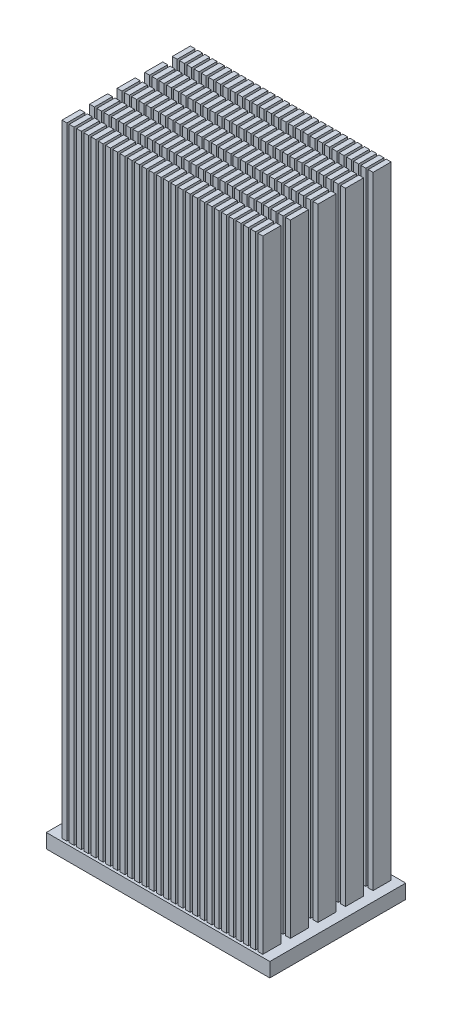
SolidWorks part; units mm, degrees
ref_plane "Front" through (0, 0, 0) normal (0, 0, 1) x (1, 0, 0)
ref_plane "Top" through (0, 0, 0) normal (0, 1, 0) x (1, 0, 0)
ref_plane "Right" through (0, 0, 0) normal (1, 0, 0) x (0, 0, -1)
sketch "Sketch1" plane through (0, 0, 0) normal (0, 1, 0) x (1, 0, 0)
  line L1 (39.12, -23.785) -> (-39.12, -23.785)
  line L2 (39.12, -23.785) -> (39.12, 23.785)
  line L3 (39.12, 23.785) -> (-39.12, 23.785)
  line L4 (-39.12, -23.785) -> (-39.12, 23.785)
  line L5 (39.12, -23.785) -> (-39.12, 23.785) construction
  line L6 (39.12, 23.785) -> (-39.12, -23.785) construction
  point P0 (0, 0)
  dimension "D1" = 47.57
  dimension "D2" = 78.24
extrude "Boss-Extrude1" add sketch "Sketch1" along normal blind 5
sketch "Sketch2" plane through (0, 0, 0) normal (0, 1, 0) x (1, 0, 0)
  line L0 (-30.3233, 22.0914) -> (-32.0273, 15.7622) construction
  line L1 (-32.8633, 22.0914) -> (-34.5673, 22.0914)
  line L2 (-32.8633, 22.0914) -> (-32.8633, 15.7622)
  line L3 (-32.8633, 15.7622) -> (-34.5673, 15.7622)
  line L4 (-34.5673, 22.0914) -> (-34.5673, 15.7622)
  line L5 (-32.8633, 22.0914) -> (-34.5673, 15.7622) construction
  line L6 (-32.8633, 15.7622) -> (-34.5673, 22.0914) construction
  line L7 (-30.3233, 15.7622) -> (-32.0273, 22.0914) construction
  line L8 (-30.3233, 22.0914) -> (-30.3233, 15.7622)
  line L9 (-30.3233, 22.0914) -> (-32.0273, 22.0914)
  line L10 (-32.0273, 22.0914) -> (-32.0273, 15.7622)
  line L11 (-30.3233, 15.7622) -> (-32.0273, 15.7622)
  line L12 (-27.7833, 22.0914) -> (-29.4873, 15.7622) construction
  line L13 (-27.7833, 15.7622) -> (-29.4873, 22.0914) construction
  line L14 (-27.7833, 22.0914) -> (-27.7833, 15.7622)
  line L15 (-27.7833, 22.0914) -> (-29.4873, 22.0914)
  line L16 (-29.4873, 22.0914) -> (-29.4873, 15.7622)
  line L17 (-27.7833, 15.7622) -> (-29.4873, 15.7622)
  line L18 (-25.2433, 22.0914) -> (-26.9473, 15.7622) construction
  line L19 (-25.2433, 15.7622) -> (-26.9473, 22.0914) construction
  line L20 (-25.2433, 22.0914) -> (-25.2433, 15.7622)
  line L21 (-25.2433, 22.0914) -> (-26.9473, 22.0914)
  line L22 (-26.9473, 22.0914) -> (-26.9473, 15.7622)
  line L23 (-25.2433, 15.7622) -> (-26.9473, 15.7622)
  line L24 (-22.7033, 22.0914) -> (-24.4073, 15.7622) construction
  line L25 (-22.7033, 15.7622) -> (-24.4073, 22.0914) construction
  line L26 (-22.7033, 22.0914) -> (-22.7033, 15.7622)
  line L27 (-22.7033, 22.0914) -> (-24.4073, 22.0914)
  line L28 (-24.4073, 22.0914) -> (-24.4073, 15.7622)
  line L29 (-22.7033, 15.7622) -> (-24.4073, 15.7622)
  line L30 (-20.1633, 22.0914) -> (-21.8673, 15.7622) construction
  line L31 (-20.1633, 15.7622) -> (-21.8673, 22.0914) construction
  line L32 (-20.1633, 22.0914) -> (-20.1633, 15.7622)
  line L33 (-20.1633, 22.0914) -> (-21.8673, 22.0914)
  line L34 (-21.8673, 22.0914) -> (-21.8673, 15.7622)
  line L35 (-20.1633, 15.7622) -> (-21.8673, 15.7622)
  line L36 (-17.6233, 22.0914) -> (-19.3273, 15.7622) construction
  line L37 (-17.6233, 15.7622) -> (-19.3273, 22.0914) construction
  line L38 (-17.6233, 22.0914) -> (-17.6233, 15.7622)
  line L39 (-17.6233, 22.0914) -> (-19.3273, 22.0914)
  line L40 (-19.3273, 22.0914) -> (-19.3273, 15.7622)
  line L41 (-17.6233, 15.7622) -> (-19.3273, 15.7622)
  line L42 (-15.0833, 22.0914) -> (-16.7873, 15.7622) construction
  line L43 (-15.0833, 15.7622) -> (-16.7873, 22.0914) construction
  line L44 (-15.0833, 22.0914) -> (-15.0833, 15.7622)
  line L45 (-15.0833, 22.0914) -> (-16.7873, 22.0914)
  line L46 (-16.7873, 22.0914) -> (-16.7873, 15.7622)
  line L47 (-15.0833, 15.7622) -> (-16.7873, 15.7622)
  line L48 (-12.5433, 22.0914) -> (-14.2473, 15.7622) construction
  line L49 (-12.5433, 15.7622) -> (-14.2473, 22.0914) construction
  line L50 (-12.5433, 22.0914) -> (-12.5433, 15.7622)
  line L51 (-12.5433, 22.0914) -> (-14.2473, 22.0914)
  line L52 (-14.2473, 22.0914) -> (-14.2473, 15.7622)
  line L53 (-12.5433, 15.7622) -> (-14.2473, 15.7622)
  line L54 (-10.0033, 22.0914) -> (-11.7073, 15.7622) construction
  line L55 (-10.0033, 15.7622) -> (-11.7073, 22.0914) construction
  line L56 (-10.0033, 22.0914) -> (-10.0033, 15.7622)
  line L57 (-10.0033, 22.0914) -> (-11.7073, 22.0914)
  line L58 (-11.7073, 22.0914) -> (-11.7073, 15.7622)
  line L59 (-10.0033, 15.7622) -> (-11.7073, 15.7622)
  line L60 (-7.4633, 22.0914) -> (-9.1673, 15.7622) construction
  line L61 (-7.4633, 15.7622) -> (-9.1673, 22.0914) construction
  line L62 (-7.4633, 22.0914) -> (-7.4633, 15.7622)
  line L63 (-7.4633, 22.0914) -> (-9.1673, 22.0914)
  line L64 (-9.1673, 22.0914) -> (-9.1673, 15.7622)
  line L65 (-7.4633, 15.7622) -> (-9.1673, 15.7622)
  line L66 (-4.9233, 22.0914) -> (-6.6273, 15.7622) construction
  line L67 (-4.9233, 15.7622) -> (-6.6273, 22.0914) construction
  line L68 (-4.9233, 22.0914) -> (-4.9233, 15.7622)
  line L69 (-4.9233, 22.0914) -> (-6.6273, 22.0914)
  line L70 (-6.6273, 22.0914) -> (-6.6273, 15.7622)
  line L71 (-4.9233, 15.7622) -> (-6.6273, 15.7622)
  line L72 (-2.3833, 22.0914) -> (-4.0873, 15.7622) construction
  line L73 (-2.3833, 15.7622) -> (-4.0873, 22.0914) construction
  line L74 (-2.3833, 22.0914) -> (-2.3833, 15.7622)
  line L75 (-2.3833, 22.0914) -> (-4.0873, 22.0914)
  line L76 (-4.0873, 22.0914) -> (-4.0873, 15.7622)
  line L77 (-2.3833, 15.7622) -> (-4.0873, 15.7622)
  line L78 (0.1567, 22.0914) -> (-1.5473, 15.7622) construction
  line L79 (0.1567, 15.7622) -> (-1.5473, 22.0914) construction
  line L80 (0.1567, 22.0914) -> (0.1567, 15.7622)
  line L81 (0.1567, 22.0914) -> (-1.5473, 22.0914)
  line L82 (-1.5473, 22.0914) -> (-1.5473, 15.7622)
  line L83 (0.1567, 15.7622) -> (-1.5473, 15.7622)
  line L84 (2.6967, 22.0914) -> (0.9927, 15.7622) construction
  line L85 (2.6967, 15.7622) -> (0.9927, 22.0914) construction
  line L86 (2.6967, 22.0914) -> (2.6967, 15.7622)
  line L87 (2.6967, 22.0914) -> (0.9927, 22.0914)
  line L88 (0.9927, 22.0914) -> (0.9927, 15.7622)
  line L89 (2.6967, 15.7622) -> (0.9927, 15.7622)
  line L90 (5.2367, 22.0914) -> (3.5327, 15.7622) construction
  line L91 (5.2367, 15.7622) -> (3.5327, 22.0914) construction
  line L92 (5.2367, 22.0914) -> (5.2367, 15.7622)
  line L93 (5.2367, 22.0914) -> (3.5327, 22.0914)
  line L94 (3.5327, 22.0914) -> (3.5327, 15.7622)
  line L95 (5.2367, 15.7622) -> (3.5327, 15.7622)
  line L96 (7.7767, 22.0914) -> (6.0727, 15.7622) construction
  line L97 (7.7767, 15.7622) -> (6.0727, 22.0914) construction
  line L98 (7.7767, 22.0914) -> (7.7767, 15.7622)
  line L99 (7.7767, 22.0914) -> (6.0727, 22.0914)
  line L100 (6.0727, 22.0914) -> (6.0727, 15.7622)
  line L101 (7.7767, 15.7622) -> (6.0727, 15.7622)
  line L102 (10.3167, 22.0914) -> (8.6127, 15.7622) construction
  line L103 (10.3167, 15.7622) -> (8.6127, 22.0914) construction
  line L104 (10.3167, 22.0914) -> (10.3167, 15.7622)
  line L105 (10.3167, 22.0914) -> (8.6127, 22.0914)
  line L106 (8.6127, 22.0914) -> (8.6127, 15.7622)
  line L107 (10.3167, 15.7622) -> (8.6127, 15.7622)
  line L108 (12.8567, 22.0914) -> (11.1527, 15.7622) construction
  line L109 (12.8567, 15.7622) -> (11.1527, 22.0914) construction
  line L110 (12.8567, 22.0914) -> (12.8567, 15.7622)
  line L111 (12.8567, 22.0914) -> (11.1527, 22.0914)
  line L112 (11.1527, 22.0914) -> (11.1527, 15.7622)
  line L113 (12.8567, 15.7622) -> (11.1527, 15.7622)
  line L114 (15.3967, 22.0914) -> (13.6927, 15.7622) construction
  line L115 (15.3967, 15.7622) -> (13.6927, 22.0914) construction
  line L116 (15.3967, 22.0914) -> (15.3967, 15.7622)
  line L117 (15.3967, 22.0914) -> (13.6927, 22.0914)
  line L118 (13.6927, 22.0914) -> (13.6927, 15.7622)
  line L119 (15.3967, 15.7622) -> (13.6927, 15.7622)
  line L120 (17.9367, 22.0914) -> (16.2327, 15.7622) construction
  line L121 (17.9367, 15.7622) -> (16.2327, 22.0914) construction
  line L122 (17.9367, 22.0914) -> (17.9367, 15.7622)
  line L123 (17.9367, 22.0914) -> (16.2327, 22.0914)
  line L124 (16.2327, 22.0914) -> (16.2327, 15.7622)
  line L125 (17.9367, 15.7622) -> (16.2327, 15.7622)
  line L126 (20.4767, 22.0914) -> (18.7727, 15.7622) construction
  line L127 (20.4767, 15.7622) -> (18.7727, 22.0914) construction
  line L128 (20.4767, 22.0914) -> (20.4767, 15.7622)
  line L129 (20.4767, 22.0914) -> (18.7727, 22.0914)
  line L130 (18.7727, 22.0914) -> (18.7727, 15.7622)
  line L131 (20.4767, 15.7622) -> (18.7727, 15.7622)
  line L132 (23.0167, 22.0914) -> (21.3127, 15.7622) construction
  line L133 (23.0167, 15.7622) -> (21.3127, 22.0914) construction
  line L134 (23.0167, 22.0914) -> (23.0167, 15.7622)
  line L135 (23.0167, 22.0914) -> (21.3127, 22.0914)
  line L136 (21.3127, 22.0914) -> (21.3127, 15.7622)
  line L137 (23.0167, 15.7622) -> (21.3127, 15.7622)
  line L138 (25.5567, 22.0914) -> (23.8527, 15.7622) construction
  line L139 (25.5567, 15.7622) -> (23.8527, 22.0914) construction
  line L140 (25.5567, 22.0914) -> (25.5567, 15.7622)
  line L141 (25.5567, 22.0914) -> (23.8527, 22.0914)
  line L142 (23.8527, 22.0914) -> (23.8527, 15.7622)
  line L143 (25.5567, 15.7622) -> (23.8527, 15.7622)
  line L144 (28.0967, 22.0914) -> (26.3927, 15.7622) construction
  line L145 (28.0967, 15.7622) -> (26.3927, 22.0914) construction
  line L146 (28.0967, 22.0914) -> (28.0967, 15.7622)
  line L147 (28.0967, 22.0914) -> (26.3927, 22.0914)
  line L148 (26.3927, 22.0914) -> (26.3927, 15.7622)
  line L149 (28.0967, 15.7622) -> (26.3927, 15.7622)
  line L150 (30.6367, 22.0914) -> (28.9327, 15.7622) construction
  line L151 (30.6367, 15.7622) -> (28.9327, 22.0914) construction
  line L152 (30.6367, 22.0914) -> (30.6367, 15.7622)
  line L153 (30.6367, 22.0914) -> (28.9327, 22.0914)
  line L154 (28.9327, 22.0914) -> (28.9327, 15.7622)
  line L155 (30.6367, 15.7622) -> (28.9327, 15.7622)
  line L156 (33.1767, 22.0914) -> (31.4727, 15.7622) construction
  line L157 (33.1767, 15.7622) -> (31.4727, 22.0914) construction
  line L158 (33.1767, 22.0914) -> (33.1767, 15.7622)
  line L159 (33.1767, 22.0914) -> (31.4727, 22.0914)
  line L160 (31.4727, 22.0914) -> (31.4727, 15.7622)
  line L161 (33.1767, 15.7622) -> (31.4727, 15.7622)
  line L162 (35.7167, 22.0914) -> (34.0127, 15.7622) construction
  line L163 (35.7167, 15.7622) -> (34.0127, 22.0914) construction
  line L164 (35.7167, 22.0914) -> (35.7167, 15.7622)
  line L165 (35.7167, 22.0914) -> (34.0127, 22.0914)
  line L166 (34.0127, 22.0914) -> (34.0127, 15.7622)
  line L167 (35.7167, 15.7622) -> (34.0127, 15.7622)
  line L168 (-30.3233, 12.4394) -> (-32.0273, 6.1102) construction
  line L169 (-30.3233, 6.1102) -> (-32.0273, 12.4394) construction
  line L170 (-30.3233, 12.4394) -> (-30.3233, 6.1102)
  line L171 (-30.3233, 12.4394) -> (-32.0273, 12.4394)
  line L172 (-32.0273, 12.4394) -> (-32.0273, 6.1102)
  line L173 (-30.3233, 6.1102) -> (-32.0273, 6.1102)
  line L174 (-27.7833, 12.4394) -> (-29.4873, 6.1102) construction
  line L175 (-27.7833, 6.1102) -> (-29.4873, 12.4394) construction
  line L176 (-27.7833, 12.4394) -> (-27.7833, 6.1102)
  line L177 (-27.7833, 12.4394) -> (-29.4873, 12.4394)
  line L178 (-29.4873, 12.4394) -> (-29.4873, 6.1102)
  line L179 (-27.7833, 6.1102) -> (-29.4873, 6.1102)
  line L180 (-25.2433, 12.4394) -> (-26.9473, 6.1102) construction
  line L181 (-25.2433, 6.1102) -> (-26.9473, 12.4394) construction
  line L182 (-25.2433, 12.4394) -> (-25.2433, 6.1102)
  line L183 (-25.2433, 12.4394) -> (-26.9473, 12.4394)
  line L184 (-26.9473, 12.4394) -> (-26.9473, 6.1102)
  line L185 (-25.2433, 6.1102) -> (-26.9473, 6.1102)
  line L186 (-22.7033, 12.4394) -> (-24.4073, 6.1102) construction
  line L187 (-22.7033, 6.1102) -> (-24.4073, 12.4394) construction
  line L188 (-22.7033, 12.4394) -> (-22.7033, 6.1102)
  line L189 (-22.7033, 12.4394) -> (-24.4073, 12.4394)
  line L190 (-24.4073, 12.4394) -> (-24.4073, 6.1102)
  line L191 (-22.7033, 6.1102) -> (-24.4073, 6.1102)
  line L192 (-20.1633, 12.4394) -> (-21.8673, 6.1102) construction
  line L193 (-20.1633, 6.1102) -> (-21.8673, 12.4394) construction
  line L194 (-20.1633, 12.4394) -> (-20.1633, 6.1102)
  line L195 (-20.1633, 12.4394) -> (-21.8673, 12.4394)
  line L196 (-21.8673, 12.4394) -> (-21.8673, 6.1102)
  line L197 (-20.1633, 6.1102) -> (-21.8673, 6.1102)
  line L198 (-17.6233, 12.4394) -> (-19.3273, 6.1102) construction
  line L199 (-17.6233, 6.1102) -> (-19.3273, 12.4394) construction
  line L200 (-17.6233, 12.4394) -> (-17.6233, 6.1102)
  line L201 (-17.6233, 12.4394) -> (-19.3273, 12.4394)
  line L202 (-19.3273, 12.4394) -> (-19.3273, 6.1102)
  line L203 (-17.6233, 6.1102) -> (-19.3273, 6.1102)
  line L204 (-15.0833, 12.4394) -> (-16.7873, 6.1102) construction
  line L205 (-15.0833, 6.1102) -> (-16.7873, 12.4394) construction
  line L206 (-15.0833, 12.4394) -> (-15.0833, 6.1102)
  line L207 (-15.0833, 12.4394) -> (-16.7873, 12.4394)
  line L208 (-16.7873, 12.4394) -> (-16.7873, 6.1102)
  line L209 (-15.0833, 6.1102) -> (-16.7873, 6.1102)
  line L210 (-12.5433, 12.4394) -> (-14.2473, 6.1102) construction
  line L211 (-12.5433, 6.1102) -> (-14.2473, 12.4394) construction
  line L212 (-12.5433, 12.4394) -> (-12.5433, 6.1102)
  line L213 (-12.5433, 12.4394) -> (-14.2473, 12.4394)
  line L214 (-14.2473, 12.4394) -> (-14.2473, 6.1102)
  line L215 (-12.5433, 6.1102) -> (-14.2473, 6.1102)
  line L216 (-10.0033, 12.4394) -> (-11.7073, 6.1102) construction
  line L217 (-10.0033, 6.1102) -> (-11.7073, 12.4394) construction
  line L218 (-10.0033, 12.4394) -> (-10.0033, 6.1102)
  line L219 (-10.0033, 12.4394) -> (-11.7073, 12.4394)
  line L220 (-11.7073, 12.4394) -> (-11.7073, 6.1102)
  line L221 (-10.0033, 6.1102) -> (-11.7073, 6.1102)
  line L222 (-7.4633, 12.4394) -> (-9.1673, 6.1102) construction
  line L223 (-7.4633, 6.1102) -> (-9.1673, 12.4394) construction
  line L224 (-7.4633, 12.4394) -> (-7.4633, 6.1102)
  line L225 (-7.4633, 12.4394) -> (-9.1673, 12.4394)
  line L226 (-9.1673, 12.4394) -> (-9.1673, 6.1102)
  line L227 (-7.4633, 6.1102) -> (-9.1673, 6.1102)
  line L228 (-4.9233, 12.4394) -> (-6.6273, 6.1102) construction
  line L229 (-4.9233, 6.1102) -> (-6.6273, 12.4394) construction
  line L230 (-4.9233, 12.4394) -> (-4.9233, 6.1102)
  line L231 (-4.9233, 12.4394) -> (-6.6273, 12.4394)
  line L232 (-6.6273, 12.4394) -> (-6.6273, 6.1102)
  line L233 (-4.9233, 6.1102) -> (-6.6273, 6.1102)
  line L234 (-2.3833, 12.4394) -> (-4.0873, 6.1102) construction
  line L235 (-2.3833, 6.1102) -> (-4.0873, 12.4394) construction
  line L236 (-2.3833, 12.4394) -> (-2.3833, 6.1102)
  line L237 (-2.3833, 12.4394) -> (-4.0873, 12.4394)
  line L238 (-4.0873, 12.4394) -> (-4.0873, 6.1102)
  line L239 (-2.3833, 6.1102) -> (-4.0873, 6.1102)
  line L240 (0.1567, 12.4394) -> (-1.5473, 6.1102) construction
  line L241 (0.1567, 6.1102) -> (-1.5473, 12.4394) construction
  line L242 (0.1567, 12.4394) -> (0.1567, 6.1102)
  line L243 (0.1567, 12.4394) -> (-1.5473, 12.4394)
  line L244 (-1.5473, 12.4394) -> (-1.5473, 6.1102)
  line L245 (0.1567, 6.1102) -> (-1.5473, 6.1102)
  line L246 (2.6967, 12.4394) -> (0.9927, 6.1102) construction
  line L247 (2.6967, 6.1102) -> (0.9927, 12.4394) construction
  line L248 (2.6967, 12.4394) -> (2.6967, 6.1102)
  line L249 (2.6967, 12.4394) -> (0.9927, 12.4394)
  line L250 (0.9927, 12.4394) -> (0.9927, 6.1102)
  line L251 (2.6967, 6.1102) -> (0.9927, 6.1102)
  line L252 (5.2367, 12.4394) -> (3.5327, 6.1102) construction
  line L253 (5.2367, 6.1102) -> (3.5327, 12.4394) construction
  line L254 (5.2367, 12.4394) -> (5.2367, 6.1102)
  line L255 (5.2367, 12.4394) -> (3.5327, 12.4394)
  line L256 (3.5327, 12.4394) -> (3.5327, 6.1102)
  line L257 (5.2367, 6.1102) -> (3.5327, 6.1102)
  line L258 (7.7767, 12.4394) -> (6.0727, 6.1102) construction
  line L259 (7.7767, 6.1102) -> (6.0727, 12.4394) construction
  line L260 (7.7767, 12.4394) -> (7.7767, 6.1102)
  line L261 (7.7767, 12.4394) -> (6.0727, 12.4394)
  line L262 (6.0727, 12.4394) -> (6.0727, 6.1102)
  line L263 (7.7767, 6.1102) -> (6.0727, 6.1102)
  line L264 (10.3167, 12.4394) -> (8.6127, 6.1102) construction
  line L265 (10.3167, 6.1102) -> (8.6127, 12.4394) construction
  line L266 (10.3167, 12.4394) -> (10.3167, 6.1102)
  line L267 (10.3167, 12.4394) -> (8.6127, 12.4394)
  line L268 (8.6127, 12.4394) -> (8.6127, 6.1102)
  line L269 (10.3167, 6.1102) -> (8.6127, 6.1102)
  line L270 (12.8567, 12.4394) -> (11.1527, 6.1102) construction
  line L271 (12.8567, 6.1102) -> (11.1527, 12.4394) construction
  line L272 (12.8567, 12.4394) -> (12.8567, 6.1102)
  line L273 (12.8567, 12.4394) -> (11.1527, 12.4394)
  line L274 (11.1527, 12.4394) -> (11.1527, 6.1102)
  line L275 (12.8567, 6.1102) -> (11.1527, 6.1102)
  line L276 (15.3967, 12.4394) -> (13.6927, 6.1102) construction
  line L277 (15.3967, 6.1102) -> (13.6927, 12.4394) construction
  line L278 (15.3967, 12.4394) -> (15.3967, 6.1102)
  line L279 (15.3967, 12.4394) -> (13.6927, 12.4394)
  line L280 (13.6927, 12.4394) -> (13.6927, 6.1102)
  line L281 (15.3967, 6.1102) -> (13.6927, 6.1102)
  line L282 (17.9367, 12.4394) -> (16.2327, 6.1102) construction
  line L283 (17.9367, 6.1102) -> (16.2327, 12.4394) construction
  line L284 (17.9367, 12.4394) -> (17.9367, 6.1102)
  line L285 (17.9367, 12.4394) -> (16.2327, 12.4394)
  line L286 (16.2327, 12.4394) -> (16.2327, 6.1102)
  line L287 (17.9367, 6.1102) -> (16.2327, 6.1102)
  line L288 (20.4767, 12.4394) -> (18.7727, 6.1102) construction
  line L289 (20.4767, 6.1102) -> (18.7727, 12.4394) construction
  line L290 (20.4767, 12.4394) -> (20.4767, 6.1102)
  line L291 (20.4767, 12.4394) -> (18.7727, 12.4394)
  line L292 (18.7727, 12.4394) -> (18.7727, 6.1102)
  line L293 (20.4767, 6.1102) -> (18.7727, 6.1102)
  line L294 (23.0167, 12.4394) -> (21.3127, 6.1102) construction
  line L295 (23.0167, 6.1102) -> (21.3127, 12.4394) construction
  line L296 (23.0167, 12.4394) -> (23.0167, 6.1102)
  line L297 (23.0167, 12.4394) -> (21.3127, 12.4394)
  line L298 (21.3127, 12.4394) -> (21.3127, 6.1102)
  line L299 (23.0167, 6.1102) -> (21.3127, 6.1102)
  line L300 (25.5567, 12.4394) -> (23.8527, 6.1102) construction
  line L301 (25.5567, 6.1102) -> (23.8527, 12.4394) construction
  line L302 (25.5567, 12.4394) -> (25.5567, 6.1102)
  line L303 (25.5567, 12.4394) -> (23.8527, 12.4394)
  line L304 (23.8527, 12.4394) -> (23.8527, 6.1102)
  line L305 (25.5567, 6.1102) -> (23.8527, 6.1102)
  line L306 (28.0967, 12.4394) -> (26.3927, 6.1102) construction
  line L307 (28.0967, 6.1102) -> (26.3927, 12.4394) construction
  line L308 (28.0967, 12.4394) -> (28.0967, 6.1102)
  line L309 (28.0967, 12.4394) -> (26.3927, 12.4394)
  line L310 (26.3927, 12.4394) -> (26.3927, 6.1102)
  line L311 (28.0967, 6.1102) -> (26.3927, 6.1102)
  line L312 (30.6367, 12.4394) -> (28.9327, 6.1102) construction
  line L313 (30.6367, 6.1102) -> (28.9327, 12.4394) construction
  line L314 (30.6367, 12.4394) -> (30.6367, 6.1102)
  line L315 (30.6367, 12.4394) -> (28.9327, 12.4394)
  line L316 (28.9327, 12.4394) -> (28.9327, 6.1102)
  line L317 (30.6367, 6.1102) -> (28.9327, 6.1102)
  line L318 (33.1767, 12.4394) -> (31.4727, 6.1102) construction
  line L319 (33.1767, 6.1102) -> (31.4727, 12.4394) construction
  line L320 (33.1767, 12.4394) -> (33.1767, 6.1102)
  line L321 (33.1767, 12.4394) -> (31.4727, 12.4394)
  line L322 (31.4727, 12.4394) -> (31.4727, 6.1102)
  line L323 (33.1767, 6.1102) -> (31.4727, 6.1102)
  line L324 (35.7167, 12.4394) -> (34.0127, 6.1102) construction
  line L325 (35.7167, 6.1102) -> (34.0127, 12.4394) construction
  line L326 (35.7167, 12.4394) -> (35.7167, 6.1102)
  line L327 (35.7167, 12.4394) -> (34.0127, 12.4394)
  line L328 (34.0127, 12.4394) -> (34.0127, 6.1102)
  line L329 (35.7167, 6.1102) -> (34.0127, 6.1102)
  line L330 (-30.3233, 2.7874) -> (-32.0273, -3.5418) construction
  line L331 (-30.3233, -3.5418) -> (-32.0273, 2.7874) construction
  line L332 (-30.3233, 2.7874) -> (-30.3233, -3.5418)
  line L333 (-30.3233, 2.7874) -> (-32.0273, 2.7874)
  line L334 (-32.0273, 2.7874) -> (-32.0273, -3.5418)
  line L335 (-30.3233, -3.5418) -> (-32.0273, -3.5418)
  line L336 (-27.7833, 2.7874) -> (-29.4873, -3.5418) construction
  line L337 (-27.7833, -3.5418) -> (-29.4873, 2.7874) construction
  line L338 (-27.7833, 2.7874) -> (-27.7833, -3.5418)
  line L339 (-27.7833, 2.7874) -> (-29.4873, 2.7874)
  line L340 (-29.4873, 2.7874) -> (-29.4873, -3.5418)
  line L341 (-27.7833, -3.5418) -> (-29.4873, -3.5418)
  line L342 (-25.2433, 2.7874) -> (-26.9473, -3.5418) construction
  line L343 (-25.2433, -3.5418) -> (-26.9473, 2.7874) construction
  line L344 (-25.2433, 2.7874) -> (-25.2433, -3.5418)
  line L345 (-25.2433, 2.7874) -> (-26.9473, 2.7874)
  line L346 (-26.9473, 2.7874) -> (-26.9473, -3.5418)
  line L347 (-25.2433, -3.5418) -> (-26.9473, -3.5418)
  line L348 (-22.7033, 2.7874) -> (-24.4073, -3.5418) construction
  line L349 (-22.7033, -3.5418) -> (-24.4073, 2.7874) construction
  line L350 (-22.7033, 2.7874) -> (-22.7033, -3.5418)
  line L351 (-22.7033, 2.7874) -> (-24.4073, 2.7874)
  line L352 (-24.4073, 2.7874) -> (-24.4073, -3.5418)
  line L353 (-22.7033, -3.5418) -> (-24.4073, -3.5418)
  line L354 (-20.1633, 2.7874) -> (-21.8673, -3.5418) construction
  line L355 (-20.1633, -3.5418) -> (-21.8673, 2.7874) construction
  line L356 (-20.1633, 2.7874) -> (-20.1633, -3.5418)
  line L357 (-20.1633, 2.7874) -> (-21.8673, 2.7874)
  line L358 (-21.8673, 2.7874) -> (-21.8673, -3.5418)
  line L359 (-20.1633, -3.5418) -> (-21.8673, -3.5418)
  line L360 (-17.6233, 2.7874) -> (-19.3273, -3.5418) construction
  line L361 (-17.6233, -3.5418) -> (-19.3273, 2.7874) construction
  line L362 (-17.6233, 2.7874) -> (-17.6233, -3.5418)
  line L363 (-17.6233, 2.7874) -> (-19.3273, 2.7874)
  line L364 (-19.3273, 2.7874) -> (-19.3273, -3.5418)
  line L365 (-17.6233, -3.5418) -> (-19.3273, -3.5418)
  line L366 (-15.0833, 2.7874) -> (-16.7873, -3.5418) construction
  line L367 (-15.0833, -3.5418) -> (-16.7873, 2.7874) construction
  line L368 (-15.0833, 2.7874) -> (-15.0833, -3.5418)
  line L369 (-15.0833, 2.7874) -> (-16.7873, 2.7874)
  line L370 (-16.7873, 2.7874) -> (-16.7873, -3.5418)
  line L371 (-15.0833, -3.5418) -> (-16.7873, -3.5418)
  line L372 (-12.5433, 2.7874) -> (-14.2473, -3.5418) construction
  line L373 (-12.5433, -3.5418) -> (-14.2473, 2.7874) construction
  line L374 (-12.5433, 2.7874) -> (-12.5433, -3.5418)
  line L375 (-12.5433, 2.7874) -> (-14.2473, 2.7874)
  line L376 (-14.2473, 2.7874) -> (-14.2473, -3.5418)
  line L377 (-12.5433, -3.5418) -> (-14.2473, -3.5418)
  line L378 (-10.0033, 2.7874) -> (-11.7073, -3.5418) construction
  line L379 (-10.0033, -3.5418) -> (-11.7073, 2.7874) construction
  line L380 (-10.0033, 2.7874) -> (-10.0033, -3.5418)
  line L381 (-10.0033, 2.7874) -> (-11.7073, 2.7874)
  line L382 (-11.7073, 2.7874) -> (-11.7073, -3.5418)
  line L383 (-10.0033, -3.5418) -> (-11.7073, -3.5418)
  line L384 (-7.4633, 2.7874) -> (-9.1673, -3.5418) construction
  line L385 (-7.4633, -3.5418) -> (-9.1673, 2.7874) construction
  line L386 (-7.4633, 2.7874) -> (-7.4633, -3.5418)
  line L387 (-7.4633, 2.7874) -> (-9.1673, 2.7874)
  line L388 (-9.1673, 2.7874) -> (-9.1673, -3.5418)
  line L389 (-7.4633, -3.5418) -> (-9.1673, -3.5418)
  line L390 (-4.9233, 2.7874) -> (-6.6273, -3.5418) construction
  line L391 (-4.9233, -3.5418) -> (-6.6273, 2.7874) construction
  line L392 (-4.9233, 2.7874) -> (-4.9233, -3.5418)
  line L393 (-4.9233, 2.7874) -> (-6.6273, 2.7874)
  line L394 (-6.6273, 2.7874) -> (-6.6273, -3.5418)
  line L395 (-4.9233, -3.5418) -> (-6.6273, -3.5418)
  line L396 (-2.3833, 2.7874) -> (-4.0873, -3.5418) construction
  line L397 (-2.3833, -3.5418) -> (-4.0873, 2.7874) construction
  line L398 (-2.3833, 2.7874) -> (-2.3833, -3.5418)
  line L399 (-2.3833, 2.7874) -> (-4.0873, 2.7874)
  line L400 (-4.0873, 2.7874) -> (-4.0873, -3.5418)
  line L401 (-2.3833, -3.5418) -> (-4.0873, -3.5418)
  line L402 (0.1567, 2.7874) -> (-1.5473, -3.5418) construction
  line L403 (0.1567, -3.5418) -> (-1.5473, 2.7874) construction
  line L404 (0.1567, 2.7874) -> (0.1567, -3.5418)
  line L405 (0.1567, 2.7874) -> (-1.5473, 2.7874)
  line L406 (-1.5473, 2.7874) -> (-1.5473, -3.5418)
  line L407 (0.1567, -3.5418) -> (-1.5473, -3.5418)
  line L408 (2.6967, 2.7874) -> (0.9927, -3.5418) construction
  line L409 (2.6967, -3.5418) -> (0.9927, 2.7874) construction
  line L410 (2.6967, 2.7874) -> (2.6967, -3.5418)
  line L411 (2.6967, 2.7874) -> (0.9927, 2.7874)
  line L412 (0.9927, 2.7874) -> (0.9927, -3.5418)
  line L413 (2.6967, -3.5418) -> (0.9927, -3.5418)
  line L414 (5.2367, 2.7874) -> (3.5327, -3.5418) construction
  line L415 (5.2367, -3.5418) -> (3.5327, 2.7874) construction
  line L416 (5.2367, 2.7874) -> (5.2367, -3.5418)
  line L417 (5.2367, 2.7874) -> (3.5327, 2.7874)
  line L418 (3.5327, 2.7874) -> (3.5327, -3.5418)
  line L419 (5.2367, -3.5418) -> (3.5327, -3.5418)
  line L420 (7.7767, 2.7874) -> (6.0727, -3.5418) construction
  line L421 (7.7767, -3.5418) -> (6.0727, 2.7874) construction
  line L422 (7.7767, 2.7874) -> (7.7767, -3.5418)
  line L423 (7.7767, 2.7874) -> (6.0727, 2.7874)
  line L424 (6.0727, 2.7874) -> (6.0727, -3.5418)
  line L425 (7.7767, -3.5418) -> (6.0727, -3.5418)
  line L426 (10.3167, 2.7874) -> (8.6127, -3.5418) construction
  line L427 (10.3167, -3.5418) -> (8.6127, 2.7874) construction
  line L428 (10.3167, 2.7874) -> (10.3167, -3.5418)
  line L429 (10.3167, 2.7874) -> (8.6127, 2.7874)
  line L430 (8.6127, 2.7874) -> (8.6127, -3.5418)
  line L431 (10.3167, -3.5418) -> (8.6127, -3.5418)
  line L432 (12.8567, 2.7874) -> (11.1527, -3.5418) construction
  line L433 (12.8567, -3.5418) -> (11.1527, 2.7874) construction
  line L434 (12.8567, 2.7874) -> (12.8567, -3.5418)
  line L435 (12.8567, 2.7874) -> (11.1527, 2.7874)
  line L436 (11.1527, 2.7874) -> (11.1527, -3.5418)
  line L437 (12.8567, -3.5418) -> (11.1527, -3.5418)
  line L438 (15.3967, 2.7874) -> (13.6927, -3.5418) construction
  line L439 (15.3967, -3.5418) -> (13.6927, 2.7874) construction
  line L440 (15.3967, 2.7874) -> (15.3967, -3.5418)
  line L441 (15.3967, 2.7874) -> (13.6927, 2.7874)
  line L442 (13.6927, 2.7874) -> (13.6927, -3.5418)
  line L443 (15.3967, -3.5418) -> (13.6927, -3.5418)
  line L444 (17.9367, 2.7874) -> (16.2327, -3.5418) construction
  line L445 (17.9367, -3.5418) -> (16.2327, 2.7874) construction
  line L446 (17.9367, 2.7874) -> (17.9367, -3.5418)
  line L447 (17.9367, 2.7874) -> (16.2327, 2.7874)
  line L448 (16.2327, 2.7874) -> (16.2327, -3.5418)
  line L449 (17.9367, -3.5418) -> (16.2327, -3.5418)
  line L450 (20.4767, 2.7874) -> (18.7727, -3.5418) construction
  line L451 (20.4767, -3.5418) -> (18.7727, 2.7874) construction
  line L452 (20.4767, 2.7874) -> (20.4767, -3.5418)
  line L453 (20.4767, 2.7874) -> (18.7727, 2.7874)
  line L454 (18.7727, 2.7874) -> (18.7727, -3.5418)
  line L455 (20.4767, -3.5418) -> (18.7727, -3.5418)
  line L456 (23.0167, 2.7874) -> (21.3127, -3.5418) construction
  line L457 (23.0167, -3.5418) -> (21.3127, 2.7874) construction
  line L458 (23.0167, 2.7874) -> (23.0167, -3.5418)
  line L459 (23.0167, 2.7874) -> (21.3127, 2.7874)
  line L460 (21.3127, 2.7874) -> (21.3127, -3.5418)
  line L461 (23.0167, -3.5418) -> (21.3127, -3.5418)
  line L462 (25.5567, 2.7874) -> (23.8527, -3.5418) construction
  line L463 (25.5567, -3.5418) -> (23.8527, 2.7874) construction
  line L464 (25.5567, 2.7874) -> (25.5567, -3.5418)
  line L465 (25.5567, 2.7874) -> (23.8527, 2.7874)
  line L466 (23.8527, 2.7874) -> (23.8527, -3.5418)
  line L467 (25.5567, -3.5418) -> (23.8527, -3.5418)
  line L468 (28.0967, 2.7874) -> (26.3927, -3.5418) construction
  line L469 (28.0967, -3.5418) -> (26.3927, 2.7874) construction
  line L470 (28.0967, 2.7874) -> (28.0967, -3.5418)
  line L471 (28.0967, 2.7874) -> (26.3927, 2.7874)
  line L472 (26.3927, 2.7874) -> (26.3927, -3.5418)
  line L473 (28.0967, -3.5418) -> (26.3927, -3.5418)
  line L474 (30.6367, 2.7874) -> (28.9327, -3.5418) construction
  line L475 (30.6367, -3.5418) -> (28.9327, 2.7874) construction
  line L476 (30.6367, 2.7874) -> (30.6367, -3.5418)
  line L477 (30.6367, 2.7874) -> (28.9327, 2.7874)
  line L478 (28.9327, 2.7874) -> (28.9327, -3.5418)
  line L479 (30.6367, -3.5418) -> (28.9327, -3.5418)
  line L480 (33.1767, 2.7874) -> (31.4727, -3.5418) construction
  line L481 (33.1767, -3.5418) -> (31.4727, 2.7874) construction
  line L482 (33.1767, 2.7874) -> (33.1767, -3.5418)
  line L483 (33.1767, 2.7874) -> (31.4727, 2.7874)
  line L484 (31.4727, 2.7874) -> (31.4727, -3.5418)
  line L485 (33.1767, -3.5418) -> (31.4727, -3.5418)
  line L486 (35.7167, 2.7874) -> (34.0127, -3.5418) construction
  line L487 (35.7167, -3.5418) -> (34.0127, 2.7874) construction
  line L488 (35.7167, 2.7874) -> (35.7167, -3.5418)
  line L489 (35.7167, 2.7874) -> (34.0127, 2.7874)
  line L490 (34.0127, 2.7874) -> (34.0127, -3.5418)
  line L491 (35.7167, -3.5418) -> (34.0127, -3.5418)
  line L492 (-30.3233, -6.8646) -> (-32.0273, -13.1938) construction
  line L493 (-30.3233, -13.1938) -> (-32.0273, -6.8646) construction
  line L494 (-30.3233, -6.8646) -> (-30.3233, -13.1938)
  line L495 (-30.3233, -6.8646) -> (-32.0273, -6.8646)
  line L496 (-32.0273, -6.8646) -> (-32.0273, -13.1938)
  line L497 (-30.3233, -13.1938) -> (-32.0273, -13.1938)
  line L498 (-27.7833, -6.8646) -> (-29.4873, -13.1938) construction
  line L499 (-27.7833, -13.1938) -> (-29.4873, -6.8646) construction
  line L500 (-27.7833, -6.8646) -> (-27.7833, -13.1938)
  line L501 (-27.7833, -6.8646) -> (-29.4873, -6.8646)
  line L502 (-29.4873, -6.8646) -> (-29.4873, -13.1938)
  line L503 (-27.7833, -13.1938) -> (-29.4873, -13.1938)
  line L504 (-25.2433, -6.8646) -> (-26.9473, -13.1938) construction
  line L505 (-25.2433, -13.1938) -> (-26.9473, -6.8646) construction
  line L506 (-25.2433, -6.8646) -> (-25.2433, -13.1938)
  line L507 (-25.2433, -6.8646) -> (-26.9473, -6.8646)
  line L508 (-26.9473, -6.8646) -> (-26.9473, -13.1938)
  line L509 (-25.2433, -13.1938) -> (-26.9473, -13.1938)
  line L510 (-22.7033, -6.8646) -> (-24.4073, -13.1938) construction
  line L511 (-22.7033, -13.1938) -> (-24.4073, -6.8646) construction
  line L512 (-22.7033, -6.8646) -> (-22.7033, -13.1938)
  line L513 (-22.7033, -6.8646) -> (-24.4073, -6.8646)
  line L514 (-24.4073, -6.8646) -> (-24.4073, -13.1938)
  line L515 (-22.7033, -13.1938) -> (-24.4073, -13.1938)
  line L516 (-20.1633, -6.8646) -> (-21.8673, -13.1938) construction
  line L517 (-20.1633, -13.1938) -> (-21.8673, -6.8646) construction
  line L518 (-20.1633, -6.8646) -> (-20.1633, -13.1938)
  line L519 (-20.1633, -6.8646) -> (-21.8673, -6.8646)
  line L520 (-21.8673, -6.8646) -> (-21.8673, -13.1938)
  line L521 (-20.1633, -13.1938) -> (-21.8673, -13.1938)
  line L522 (-17.6233, -6.8646) -> (-19.3273, -13.1938) construction
  line L523 (-17.6233, -13.1938) -> (-19.3273, -6.8646) construction
  line L524 (-17.6233, -6.8646) -> (-17.6233, -13.1938)
  line L525 (-17.6233, -6.8646) -> (-19.3273, -6.8646)
  line L526 (-19.3273, -6.8646) -> (-19.3273, -13.1938)
  line L527 (-17.6233, -13.1938) -> (-19.3273, -13.1938)
  line L528 (-15.0833, -6.8646) -> (-16.7873, -13.1938) construction
  line L529 (-15.0833, -13.1938) -> (-16.7873, -6.8646) construction
  line L530 (-15.0833, -6.8646) -> (-15.0833, -13.1938)
  line L531 (-15.0833, -6.8646) -> (-16.7873, -6.8646)
  line L532 (-16.7873, -6.8646) -> (-16.7873, -13.1938)
  line L533 (-15.0833, -13.1938) -> (-16.7873, -13.1938)
  line L534 (-12.5433, -6.8646) -> (-14.2473, -13.1938) construction
  line L535 (-12.5433, -13.1938) -> (-14.2473, -6.8646) construction
  line L536 (-12.5433, -6.8646) -> (-12.5433, -13.1938)
  line L537 (-12.5433, -6.8646) -> (-14.2473, -6.8646)
  line L538 (-14.2473, -6.8646) -> (-14.2473, -13.1938)
  line L539 (-12.5433, -13.1938) -> (-14.2473, -13.1938)
  line L540 (-10.0033, -6.8646) -> (-11.7073, -13.1938) construction
  line L541 (-10.0033, -13.1938) -> (-11.7073, -6.8646) construction
  line L542 (-10.0033, -6.8646) -> (-10.0033, -13.1938)
  line L543 (-10.0033, -6.8646) -> (-11.7073, -6.8646)
  line L544 (-11.7073, -6.8646) -> (-11.7073, -13.1938)
  line L545 (-10.0033, -13.1938) -> (-11.7073, -13.1938)
  line L546 (-7.4633, -6.8646) -> (-9.1673, -13.1938) construction
  line L547 (-7.4633, -13.1938) -> (-9.1673, -6.8646) construction
  line L548 (-7.4633, -6.8646) -> (-7.4633, -13.1938)
  line L549 (-7.4633, -6.8646) -> (-9.1673, -6.8646)
  line L550 (-9.1673, -6.8646) -> (-9.1673, -13.1938)
  line L551 (-7.4633, -13.1938) -> (-9.1673, -13.1938)
  line L552 (-4.9233, -6.8646) -> (-6.6273, -13.1938) construction
  line L553 (-4.9233, -13.1938) -> (-6.6273, -6.8646) construction
  line L554 (-4.9233, -6.8646) -> (-4.9233, -13.1938)
  line L555 (-4.9233, -6.8646) -> (-6.6273, -6.8646)
  line L556 (-6.6273, -6.8646) -> (-6.6273, -13.1938)
  line L557 (-4.9233, -13.1938) -> (-6.6273, -13.1938)
  line L558 (-2.3833, -6.8646) -> (-4.0873, -13.1938) construction
  line L559 (-2.3833, -13.1938) -> (-4.0873, -6.8646) construction
  line L560 (-2.3833, -6.8646) -> (-2.3833, -13.1938)
  line L561 (-2.3833, -6.8646) -> (-4.0873, -6.8646)
  line L562 (-4.0873, -6.8646) -> (-4.0873, -13.1938)
  line L563 (-2.3833, -13.1938) -> (-4.0873, -13.1938)
  line L564 (0.1567, -6.8646) -> (-1.5473, -13.1938) construction
  line L565 (0.1567, -13.1938) -> (-1.5473, -6.8646) construction
  line L566 (0.1567, -6.8646) -> (0.1567, -13.1938)
  line L567 (0.1567, -6.8646) -> (-1.5473, -6.8646)
  line L568 (-1.5473, -6.8646) -> (-1.5473, -13.1938)
  line L569 (0.1567, -13.1938) -> (-1.5473, -13.1938)
  line L570 (2.6967, -6.8646) -> (0.9927, -13.1938) construction
  line L571 (2.6967, -13.1938) -> (0.9927, -6.8646) construction
  line L572 (2.6967, -6.8646) -> (2.6967, -13.1938)
  line L573 (2.6967, -6.8646) -> (0.9927, -6.8646)
  line L574 (0.9927, -6.8646) -> (0.9927, -13.1938)
  line L575 (2.6967, -13.1938) -> (0.9927, -13.1938)
  line L576 (5.2367, -6.8646) -> (3.5327, -13.1938) construction
  line L577 (5.2367, -13.1938) -> (3.5327, -6.8646) construction
  line L578 (5.2367, -6.8646) -> (5.2367, -13.1938)
  line L579 (5.2367, -6.8646) -> (3.5327, -6.8646)
  line L580 (3.5327, -6.8646) -> (3.5327, -13.1938)
  line L581 (5.2367, -13.1938) -> (3.5327, -13.1938)
  line L582 (7.7767, -6.8646) -> (6.0727, -13.1938) construction
  line L583 (7.7767, -13.1938) -> (6.0727, -6.8646) construction
  line L584 (7.7767, -6.8646) -> (7.7767, -13.1938)
  line L585 (7.7767, -6.8646) -> (6.0727, -6.8646)
  line L586 (6.0727, -6.8646) -> (6.0727, -13.1938)
  line L587 (7.7767, -13.1938) -> (6.0727, -13.1938)
  line L588 (10.3167, -6.8646) -> (8.6127, -13.1938) construction
  line L589 (10.3167, -13.1938) -> (8.6127, -6.8646) construction
  line L590 (10.3167, -6.8646) -> (10.3167, -13.1938)
  line L591 (10.3167, -6.8646) -> (8.6127, -6.8646)
  line L592 (8.6127, -6.8646) -> (8.6127, -13.1938)
  line L593 (10.3167, -13.1938) -> (8.6127, -13.1938)
  line L594 (12.8567, -6.8646) -> (11.1527, -13.1938) construction
  line L595 (12.8567, -13.1938) -> (11.1527, -6.8646) construction
  line L596 (12.8567, -6.8646) -> (12.8567, -13.1938)
  line L597 (12.8567, -6.8646) -> (11.1527, -6.8646)
  line L598 (11.1527, -6.8646) -> (11.1527, -13.1938)
  line L599 (12.8567, -13.1938) -> (11.1527, -13.1938)
  line L600 (15.3967, -6.8646) -> (13.6927, -13.1938) construction
  line L601 (15.3967, -13.1938) -> (13.6927, -6.8646) construction
  line L602 (15.3967, -6.8646) -> (15.3967, -13.1938)
  line L603 (15.3967, -6.8646) -> (13.6927, -6.8646)
  line L604 (13.6927, -6.8646) -> (13.6927, -13.1938)
  line L605 (15.3967, -13.1938) -> (13.6927, -13.1938)
  line L606 (17.9367, -6.8646) -> (16.2327, -13.1938) construction
  line L607 (17.9367, -13.1938) -> (16.2327, -6.8646) construction
  line L608 (17.9367, -6.8646) -> (17.9367, -13.1938)
  line L609 (17.9367, -6.8646) -> (16.2327, -6.8646)
  line L610 (16.2327, -6.8646) -> (16.2327, -13.1938)
  line L611 (17.9367, -13.1938) -> (16.2327, -13.1938)
  line L612 (20.4767, -6.8646) -> (18.7727, -13.1938) construction
  line L613 (20.4767, -13.1938) -> (18.7727, -6.8646) construction
  line L614 (20.4767, -6.8646) -> (20.4767, -13.1938)
  line L615 (20.4767, -6.8646) -> (18.7727, -6.8646)
  line L616 (18.7727, -6.8646) -> (18.7727, -13.1938)
  line L617 (20.4767, -13.1938) -> (18.7727, -13.1938)
  line L618 (23.0167, -6.8646) -> (21.3127, -13.1938) construction
  line L619 (23.0167, -13.1938) -> (21.3127, -6.8646) construction
  line L620 (23.0167, -6.8646) -> (23.0167, -13.1938)
  line L621 (23.0167, -6.8646) -> (21.3127, -6.8646)
  line L622 (21.3127, -6.8646) -> (21.3127, -13.1938)
  line L623 (23.0167, -13.1938) -> (21.3127, -13.1938)
  line L624 (25.5567, -6.8646) -> (23.8527, -13.1938) construction
  line L625 (25.5567, -13.1938) -> (23.8527, -6.8646) construction
  line L626 (25.5567, -6.8646) -> (25.5567, -13.1938)
  line L627 (25.5567, -6.8646) -> (23.8527, -6.8646)
  line L628 (23.8527, -6.8646) -> (23.8527, -13.1938)
  line L629 (25.5567, -13.1938) -> (23.8527, -13.1938)
  line L630 (28.0967, -6.8646) -> (26.3927, -13.1938) construction
  line L631 (28.0967, -13.1938) -> (26.3927, -6.8646) construction
  line L632 (28.0967, -6.8646) -> (28.0967, -13.1938)
  line L633 (28.0967, -6.8646) -> (26.3927, -6.8646)
  line L634 (26.3927, -6.8646) -> (26.3927, -13.1938)
  line L635 (28.0967, -13.1938) -> (26.3927, -13.1938)
  line L636 (30.6367, -6.8646) -> (28.9327, -13.1938) construction
  line L637 (30.6367, -13.1938) -> (28.9327, -6.8646) construction
  line L638 (30.6367, -6.8646) -> (30.6367, -13.1938)
  line L639 (30.6367, -6.8646) -> (28.9327, -6.8646)
  line L640 (28.9327, -6.8646) -> (28.9327, -13.1938)
  line L641 (30.6367, -13.1938) -> (28.9327, -13.1938)
  line L642 (33.1767, -6.8646) -> (31.4727, -13.1938) construction
  line L643 (33.1767, -13.1938) -> (31.4727, -6.8646) construction
  line L644 (33.1767, -6.8646) -> (33.1767, -13.1938)
  line L645 (33.1767, -6.8646) -> (31.4727, -6.8646)
  line L646 (31.4727, -6.8646) -> (31.4727, -13.1938)
  line L647 (33.1767, -13.1938) -> (31.4727, -13.1938)
  line L648 (35.7167, -6.8646) -> (34.0127, -13.1938) construction
  line L649 (35.7167, -13.1938) -> (34.0127, -6.8646) construction
  line L650 (35.7167, -6.8646) -> (35.7167, -13.1938)
  line L651 (35.7167, -6.8646) -> (34.0127, -6.8646)
  line L652 (34.0127, -6.8646) -> (34.0127, -13.1938)
  line L653 (35.7167, -13.1938) -> (34.0127, -13.1938)
  line L654 (-30.3233, -16.5166) -> (-32.0273, -22.8458) construction
  line L655 (-30.3233, -22.8458) -> (-32.0273, -16.5166) construction
  line L656 (-30.3233, -16.5166) -> (-30.3233, -22.8458)
  line L657 (-30.3233, -16.5166) -> (-32.0273, -16.5166)
  line L658 (-32.0273, -16.5166) -> (-32.0273, -22.8458)
  line L659 (-30.3233, -22.8458) -> (-32.0273, -22.8458)
  line L660 (-27.7833, -16.5166) -> (-29.4873, -22.8458) construction
  line L661 (-27.7833, -22.8458) -> (-29.4873, -16.5166) construction
  line L662 (-27.7833, -16.5166) -> (-27.7833, -22.8458)
  line L663 (-27.7833, -16.5166) -> (-29.4873, -16.5166)
  line L664 (-29.4873, -16.5166) -> (-29.4873, -22.8458)
  line L665 (-27.7833, -22.8458) -> (-29.4873, -22.8458)
  line L666 (-25.2433, -16.5166) -> (-26.9473, -22.8458) construction
  line L667 (-25.2433, -22.8458) -> (-26.9473, -16.5166) construction
  line L668 (-25.2433, -16.5166) -> (-25.2433, -22.8458)
  line L669 (-25.2433, -16.5166) -> (-26.9473, -16.5166)
  line L670 (-26.9473, -16.5166) -> (-26.9473, -22.8458)
  line L671 (-25.2433, -22.8458) -> (-26.9473, -22.8458)
  line L672 (-22.7033, -16.5166) -> (-24.4073, -22.8458) construction
  line L673 (-22.7033, -22.8458) -> (-24.4073, -16.5166) construction
  line L674 (-22.7033, -16.5166) -> (-22.7033, -22.8458)
  line L675 (-22.7033, -16.5166) -> (-24.4073, -16.5166)
  line L676 (-24.4073, -16.5166) -> (-24.4073, -22.8458)
  line L677 (-22.7033, -22.8458) -> (-24.4073, -22.8458)
  line L678 (-20.1633, -16.5166) -> (-21.8673, -22.8458) construction
  line L679 (-20.1633, -22.8458) -> (-21.8673, -16.5166) construction
  line L680 (-20.1633, -16.5166) -> (-20.1633, -22.8458)
  line L681 (-20.1633, -16.5166) -> (-21.8673, -16.5166)
  line L682 (-21.8673, -16.5166) -> (-21.8673, -22.8458)
  line L683 (-20.1633, -22.8458) -> (-21.8673, -22.8458)
  line L684 (-17.6233, -16.5166) -> (-19.3273, -22.8458) construction
  line L685 (-17.6233, -22.8458) -> (-19.3273, -16.5166) construction
  line L686 (-17.6233, -16.5166) -> (-17.6233, -22.8458)
  line L687 (-17.6233, -16.5166) -> (-19.3273, -16.5166)
  line L688 (-19.3273, -16.5166) -> (-19.3273, -22.8458)
  line L689 (-17.6233, -22.8458) -> (-19.3273, -22.8458)
  line L690 (-15.0833, -16.5166) -> (-16.7873, -22.8458) construction
  line L691 (-15.0833, -22.8458) -> (-16.7873, -16.5166) construction
  line L692 (-15.0833, -16.5166) -> (-15.0833, -22.8458)
  line L693 (-15.0833, -16.5166) -> (-16.7873, -16.5166)
  line L694 (-16.7873, -16.5166) -> (-16.7873, -22.8458)
  line L695 (-15.0833, -22.8458) -> (-16.7873, -22.8458)
  line L696 (-12.5433, -16.5166) -> (-14.2473, -22.8458) construction
  line L697 (-12.5433, -22.8458) -> (-14.2473, -16.5166) construction
  line L698 (-12.5433, -16.5166) -> (-12.5433, -22.8458)
  line L699 (-12.5433, -16.5166) -> (-14.2473, -16.5166)
  line L700 (-14.2473, -16.5166) -> (-14.2473, -22.8458)
  line L701 (-12.5433, -22.8458) -> (-14.2473, -22.8458)
  line L702 (-10.0033, -16.5166) -> (-11.7073, -22.8458) construction
  line L703 (-10.0033, -22.8458) -> (-11.7073, -16.5166) construction
  line L704 (-10.0033, -16.5166) -> (-10.0033, -22.8458)
  line L705 (-10.0033, -16.5166) -> (-11.7073, -16.5166)
  line L706 (-11.7073, -16.5166) -> (-11.7073, -22.8458)
  line L707 (-10.0033, -22.8458) -> (-11.7073, -22.8458)
  line L708 (-7.4633, -16.5166) -> (-9.1673, -22.8458) construction
  line L709 (-7.4633, -22.8458) -> (-9.1673, -16.5166) construction
  line L710 (-7.4633, -16.5166) -> (-7.4633, -22.8458)
  line L711 (-7.4633, -16.5166) -> (-9.1673, -16.5166)
  line L712 (-9.1673, -16.5166) -> (-9.1673, -22.8458)
  line L713 (-7.4633, -22.8458) -> (-9.1673, -22.8458)
  line L714 (-4.9233, -16.5166) -> (-6.6273, -22.8458) construction
  line L715 (-4.9233, -22.8458) -> (-6.6273, -16.5166) construction
  line L716 (-4.9233, -16.5166) -> (-4.9233, -22.8458)
  line L717 (-4.9233, -16.5166) -> (-6.6273, -16.5166)
  line L718 (-6.6273, -16.5166) -> (-6.6273, -22.8458)
  line L719 (-4.9233, -22.8458) -> (-6.6273, -22.8458)
  line L720 (-2.3833, -16.5166) -> (-4.0873, -22.8458) construction
  line L721 (-2.3833, -22.8458) -> (-4.0873, -16.5166) construction
  line L722 (-2.3833, -16.5166) -> (-2.3833, -22.8458)
  line L723 (-2.3833, -16.5166) -> (-4.0873, -16.5166)
  line L724 (-4.0873, -16.5166) -> (-4.0873, -22.8458)
  line L725 (-2.3833, -22.8458) -> (-4.0873, -22.8458)
  line L726 (0.1567, -16.5166) -> (-1.5473, -22.8458) construction
  line L727 (0.1567, -22.8458) -> (-1.5473, -16.5166) construction
  line L728 (0.1567, -16.5166) -> (0.1567, -22.8458)
  line L729 (0.1567, -16.5166) -> (-1.5473, -16.5166)
  line L730 (-1.5473, -16.5166) -> (-1.5473, -22.8458)
  line L731 (0.1567, -22.8458) -> (-1.5473, -22.8458)
  line L732 (2.6967, -16.5166) -> (0.9927, -22.8458) construction
  line L733 (2.6967, -22.8458) -> (0.9927, -16.5166) construction
  line L734 (2.6967, -16.5166) -> (2.6967, -22.8458)
  line L735 (2.6967, -16.5166) -> (0.9927, -16.5166)
  line L736 (0.9927, -16.5166) -> (0.9927, -22.8458)
  line L737 (2.6967, -22.8458) -> (0.9927, -22.8458)
  line L738 (5.2367, -16.5166) -> (3.5327, -22.8458) construction
  line L739 (5.2367, -22.8458) -> (3.5327, -16.5166) construction
  line L740 (5.2367, -16.5166) -> (5.2367, -22.8458)
  line L741 (5.2367, -16.5166) -> (3.5327, -16.5166)
  line L742 (3.5327, -16.5166) -> (3.5327, -22.8458)
  line L743 (5.2367, -22.8458) -> (3.5327, -22.8458)
  line L744 (7.7767, -16.5166) -> (6.0727, -22.8458) construction
  line L745 (7.7767, -22.8458) -> (6.0727, -16.5166) construction
  line L746 (7.7767, -16.5166) -> (7.7767, -22.8458)
  line L747 (7.7767, -16.5166) -> (6.0727, -16.5166)
  line L748 (6.0727, -16.5166) -> (6.0727, -22.8458)
  line L749 (7.7767, -22.8458) -> (6.0727, -22.8458)
  line L750 (10.3167, -16.5166) -> (8.6127, -22.8458) construction
  line L751 (10.3167, -22.8458) -> (8.6127, -16.5166) construction
  line L752 (10.3167, -16.5166) -> (10.3167, -22.8458)
  line L753 (10.3167, -16.5166) -> (8.6127, -16.5166)
  line L754 (8.6127, -16.5166) -> (8.6127, -22.8458)
  line L755 (10.3167, -22.8458) -> (8.6127, -22.8458)
  line L756 (12.8567, -16.5166) -> (11.1527, -22.8458) construction
  line L757 (12.8567, -22.8458) -> (11.1527, -16.5166) construction
  line L758 (12.8567, -16.5166) -> (12.8567, -22.8458)
  line L759 (12.8567, -16.5166) -> (11.1527, -16.5166)
  line L760 (11.1527, -16.5166) -> (11.1527, -22.8458)
  line L761 (12.8567, -22.8458) -> (11.1527, -22.8458)
  line L762 (15.3967, -16.5166) -> (13.6927, -22.8458) construction
  line L763 (15.3967, -22.8458) -> (13.6927, -16.5166) construction
  line L764 (15.3967, -16.5166) -> (15.3967, -22.8458)
  line L765 (15.3967, -16.5166) -> (13.6927, -16.5166)
  line L766 (13.6927, -16.5166) -> (13.6927, -22.8458)
  line L767 (15.3967, -22.8458) -> (13.6927, -22.8458)
  line L768 (17.9367, -16.5166) -> (16.2327, -22.8458) construction
  line L769 (17.9367, -22.8458) -> (16.2327, -16.5166) construction
  line L770 (17.9367, -16.5166) -> (17.9367, -22.8458)
  line L771 (17.9367, -16.5166) -> (16.2327, -16.5166)
  line L772 (16.2327, -16.5166) -> (16.2327, -22.8458)
  line L773 (17.9367, -22.8458) -> (16.2327, -22.8458)
  line L774 (20.4767, -16.5166) -> (18.7727, -22.8458) construction
  line L775 (20.4767, -22.8458) -> (18.7727, -16.5166) construction
  line L776 (20.4767, -16.5166) -> (20.4767, -22.8458)
  line L777 (20.4767, -16.5166) -> (18.7727, -16.5166)
  line L778 (18.7727, -16.5166) -> (18.7727, -22.8458)
  line L779 (20.4767, -22.8458) -> (18.7727, -22.8458)
  line L780 (23.0167, -16.5166) -> (21.3127, -22.8458) construction
  line L781 (23.0167, -22.8458) -> (21.3127, -16.5166) construction
  line L782 (23.0167, -16.5166) -> (23.0167, -22.8458)
  line L783 (23.0167, -16.5166) -> (21.3127, -16.5166)
  line L784 (21.3127, -16.5166) -> (21.3127, -22.8458)
  line L785 (23.0167, -22.8458) -> (21.3127, -22.8458)
  line L786 (25.5567, -16.5166) -> (23.8527, -22.8458) construction
  line L787 (25.5567, -22.8458) -> (23.8527, -16.5166) construction
  line L788 (25.5567, -16.5166) -> (25.5567, -22.8458)
  line L789 (25.5567, -16.5166) -> (23.8527, -16.5166)
  line L790 (23.8527, -16.5166) -> (23.8527, -22.8458)
  line L791 (25.5567, -22.8458) -> (23.8527, -22.8458)
  line L792 (28.0967, -16.5166) -> (26.3927, -22.8458) construction
  line L793 (28.0967, -22.8458) -> (26.3927, -16.5166) construction
  line L794 (28.0967, -16.5166) -> (28.0967, -22.8458)
  line L795 (28.0967, -16.5166) -> (26.3927, -16.5166)
  line L796 (26.3927, -16.5166) -> (26.3927, -22.8458)
  line L797 (28.0967, -22.8458) -> (26.3927, -22.8458)
  line L798 (30.6367, -16.5166) -> (28.9327, -22.8458) construction
  line L799 (30.6367, -22.8458) -> (28.9327, -16.5166) construction
  line L800 (30.6367, -16.5166) -> (30.6367, -22.8458)
  line L801 (30.6367, -16.5166) -> (28.9327, -16.5166)
  line L802 (28.9327, -16.5166) -> (28.9327, -22.8458)
  line L803 (30.6367, -22.8458) -> (28.9327, -22.8458)
  line L804 (33.1767, -16.5166) -> (31.4727, -22.8458) construction
  line L805 (33.1767, -22.8458) -> (31.4727, -16.5166) construction
  line L806 (33.1767, -16.5166) -> (33.1767, -22.8458)
  line L807 (33.1767, -16.5166) -> (31.4727, -16.5166)
  line L808 (31.4727, -16.5166) -> (31.4727, -22.8458)
  line L809 (33.1767, -22.8458) -> (31.4727, -22.8458)
  line L810 (35.7167, -16.5166) -> (34.0127, -22.8458) construction
  line L811 (35.7167, -22.8458) -> (34.0127, -16.5166) construction
  line L812 (35.7167, -16.5166) -> (35.7167, -22.8458)
  line L813 (35.7167, -16.5166) -> (34.0127, -16.5166)
  line L814 (34.0127, -16.5166) -> (34.0127, -22.8458)
  line L815 (35.7167, -22.8458) -> (34.0127, -22.8458)
  line L816 (-32.8633, 12.4394) -> (-34.5673, 6.1102) construction
  line L817 (-32.8633, 6.1102) -> (-34.5673, 12.4394) construction
  line L818 (-32.8633, 12.4394) -> (-32.8633, 6.1102)
  line L819 (-32.8633, 12.4394) -> (-34.5673, 12.4394)
  line L820 (-34.5673, 12.4394) -> (-34.5673, 6.1102)
  line L821 (-32.8633, 6.1102) -> (-34.5673, 6.1102)
  line L822 (-32.8633, 2.7874) -> (-34.5673, -3.5418) construction
  line L823 (-32.8633, -3.5418) -> (-34.5673, 2.7874) construction
  line L824 (-32.8633, 2.7874) -> (-32.8633, -3.5418)
  line L825 (-32.8633, 2.7874) -> (-34.5673, 2.7874)
  line L826 (-34.5673, 2.7874) -> (-34.5673, -3.5418)
  line L827 (-32.8633, -3.5418) -> (-34.5673, -3.5418)
  line L828 (-32.8633, -6.8646) -> (-34.5673, -13.1938) construction
  line L829 (-32.8633, -13.1938) -> (-34.5673, -6.8646) construction
  line L830 (-32.8633, -6.8646) -> (-32.8633, -13.1938)
  line L831 (-32.8633, -6.8646) -> (-34.5673, -6.8646)
  line L832 (-34.5673, -6.8646) -> (-34.5673, -13.1938)
  line L833 (-32.8633, -13.1938) -> (-34.5673, -13.1938)
  line L834 (-32.8633, -16.5166) -> (-34.5673, -22.8458) construction
  line L835 (-32.8633, -22.8458) -> (-34.5673, -16.5166) construction
  line L836 (-32.8633, -16.5166) -> (-32.8633, -22.8458)
  line L837 (-32.8633, -16.5166) -> (-34.5673, -16.5166)
  line L838 (-34.5673, -16.5166) -> (-34.5673, -22.8458)
  line L839 (-32.8633, -22.8458) -> (-34.5673, -22.8458)
  point P0 (-33.7153, 18.9268)
  point P6 (-31.1753, 18.9268)
  point P12 (-28.6353, 18.9268)
  point P17 (-26.0953, 18.9268)
  point P22 (-23.5553, 18.9268)
  point P27 (-21.0153, 18.9268)
  point P32 (-18.4753, 18.9268)
  point P37 (-15.9353, 18.9268)
  point P42 (-13.3953, 18.9268)
  point P47 (-10.8553, 18.9268)
  point P52 (-8.3153, 18.9268)
  point P57 (-5.7753, 18.9268)
  point P62 (-3.2353, 18.9268)
  point P67 (-0.6953, 18.9268)
  point P72 (1.8447, 18.9268)
  point P77 (4.3847, 18.9268)
  point P82 (6.9247, 18.9268)
  point P87 (9.4647, 18.9268)
  point P92 (12.0047, 18.9268)
  point P97 (14.5447, 18.9268)
  point P102 (17.0847, 18.9268)
  point P107 (19.6247, 18.9268)
  point P112 (22.1647, 18.9268)
  point P117 (24.7047, 18.9268)
  point P122 (27.2447, 18.9268)
  point P127 (29.7847, 18.9268)
  point P132 (32.3247, 18.9268)
  point P137 (34.8647, 18.9268)
  point P142 (-31.1753, 9.2748)
  point P147 (-28.6353, 9.2748)
  point P152 (-26.0953, 9.2748)
  point P157 (-23.5553, 9.2748)
  point P162 (-21.0153, 9.2748)
  point P167 (-18.4753, 9.2748)
  point P172 (-15.9353, 9.2748)
  point P177 (-13.3953, 9.2748)
  point P182 (-10.8553, 9.2748)
  point P187 (-8.3153, 9.2748)
  point P192 (-5.7753, 9.2748)
  point P197 (-3.2353, 9.2748)
  point P202 (-0.6953, 9.2748)
  point P207 (1.8447, 9.2748)
  point P212 (4.3847, 9.2748)
  point P217 (6.9247, 9.2748)
  point P222 (9.4647, 9.2748)
  point P227 (12.0047, 9.2748)
  point P232 (14.5447, 9.2748)
  point P237 (17.0847, 9.2748)
  point P242 (19.6247, 9.2748)
  point P247 (22.1647, 9.2748)
  point P252 (24.7047, 9.2748)
  point P257 (27.2447, 9.2748)
  point P262 (29.7847, 9.2748)
  point P267 (32.3247, 9.2748)
  point P272 (34.8647, 9.2748)
  point P277 (-31.1753, -0.3772)
  point P282 (-28.6353, -0.3772)
  point P287 (-26.0953, -0.3772)
  point P292 (-23.5553, -0.3772)
  point P297 (-21.0153, -0.3772)
  point P302 (-18.4753, -0.3772)
  point P307 (-15.9353, -0.3772)
  point P312 (-13.3953, -0.3772)
  point P317 (-10.8553, -0.3772)
  point P322 (-8.3153, -0.3772)
  point P327 (-5.7753, -0.3772)
  point P332 (-3.2353, -0.3772)
  point P337 (-0.6953, -0.3772)
  point P342 (1.8447, -0.3772)
  point P347 (4.3847, -0.3772)
  point P352 (6.9247, -0.3772)
  point P357 (9.4647, -0.3772)
  point P362 (12.0047, -0.3772)
  point P367 (14.5447, -0.3772)
  point P372 (17.0847, -0.3772)
  point P377 (19.6247, -0.3772)
  point P382 (22.1647, -0.3772)
  point P387 (24.7047, -0.3772)
  point P392 (27.2447, -0.3772)
  point P397 (29.7847, -0.3772)
  point P402 (32.3247, -0.3772)
  point P407 (34.8647, -0.3772)
  point P412 (-31.1753, -10.0292)
  point P417 (-28.6353, -10.0292)
  point P422 (-26.0953, -10.0292)
  point P427 (-23.5553, -10.0292)
  point P432 (-21.0153, -10.0292)
  point P437 (-18.4753, -10.0292)
  point P442 (-15.9353, -10.0292)
  point P447 (-13.3953, -10.0292)
  point P452 (-10.8553, -10.0292)
  point P457 (-8.3153, -10.0292)
  point P462 (-5.7753, -10.0292)
  point P467 (-3.2353, -10.0292)
  point P472 (-0.6953, -10.0292)
  point P477 (1.8447, -10.0292)
  point P482 (4.3847, -10.0292)
  point P487 (6.9247, -10.0292)
  point P492 (9.4647, -10.0292)
  point P497 (12.0047, -10.0292)
  point P502 (14.5447, -10.0292)
  point P507 (17.0847, -10.0292)
  point P512 (19.6247, -10.0292)
  point P517 (22.1647, -10.0292)
  point P522 (24.7047, -10.0292)
  point P527 (27.2447, -10.0292)
  point P532 (29.7847, -10.0292)
  point P537 (32.3247, -10.0292)
  point P542 (34.8647, -10.0292)
  point P547 (-31.1753, -19.6812)
  point P552 (-28.6353, -19.6812)
  point P557 (-26.0953, -19.6812)
  point P562 (-23.5553, -19.6812)
  point P567 (-21.0153, -19.6812)
  point P572 (-18.4753, -19.6812)
  point P577 (-15.9353, -19.6812)
  point P582 (-13.3953, -19.6812)
  point P587 (-10.8553, -19.6812)
  point P592 (-8.3153, -19.6812)
  point P597 (-5.7753, -19.6812)
  point P602 (-3.2353, -19.6812)
  point P607 (-0.6953, -19.6812)
  point P612 (1.8447, -19.6812)
  point P617 (4.3847, -19.6812)
  point P622 (6.9247, -19.6812)
  point P627 (9.4647, -19.6812)
  point P632 (12.0047, -19.6812)
  point P637 (14.5447, -19.6812)
  point P642 (17.0847, -19.6812)
  point P647 (19.6247, -19.6812)
  point P652 (22.1647, -19.6812)
  point P657 (24.7047, -19.6812)
  point P662 (27.2447, -19.6812)
  point P667 (29.7847, -19.6812)
  point P672 (32.3247, -19.6812)
  point P677 (34.8647, -19.6812)
  point P682 (-33.7153, 9.2748)
  point P687 (-33.7153, -0.3772)
  point P692 (-33.7153, -10.0292)
  point P697 (-33.7153, -19.6812)
  dimension "D1" = 28
  dimension "D2" = 5
extrude "Boss-Extrude2" add sketch "Sketch2" along normal blind 222.758
